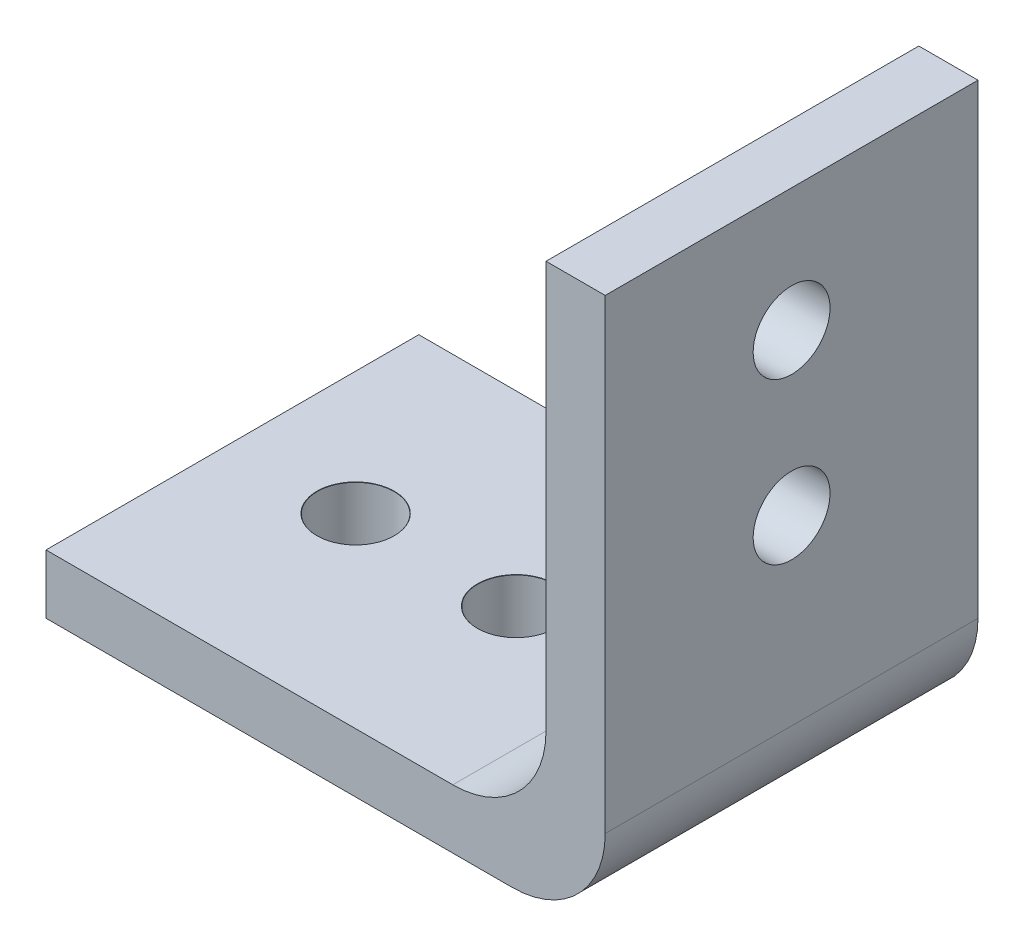
SolidWorks part; units mm, degrees
ref_plane "Front Plane" through (0, 0, 0) normal (0, 0, 1) x (1, 0, 0)
ref_plane "Top Plane" through (0, 0, 0) normal (0, 1, 0) x (1, 0, 0)
ref_plane "Right Plane" through (0, 0, 0) normal (1, 0, 0) x (0, 0, -1)
sketch "Sketch1" plane through (0, 0, 0) normal (0, 1, 0) x (1, 0, 0)
  line L1 (-18.3871, 16.4043) -> (41.6129, 16.4043)
  line L2 (-18.3871, 16.4043) -> (-18.3871, -23.5957)
  line L3 (-18.3871, -23.5957) -> (41.6129, -23.5957)
  line L4 (41.6129, 16.4043) -> (41.6129, -23.5957)
  dimension "D1" = 60
  dimension "D2" = 40
  dimension "D3" = 18.3871
  dimension "D4" = 16.4043
extrude "Boss-Extrude1" add sketch "Sketch1" along normal blind 6.35
sketch "Sketch2" plane through (0, 6.35, 0) normal (0, 1, 0) x (1, 0, 0)
  line L0 (41.6129, 16.4043) -> (-18.3871, 16.4043) construction
  line L1 (35.2629, 16.4043) -> (41.6129, 16.4043)
  line L2 (35.2629, 16.4043) -> (35.2629, -23.5957)
  line L3 (35.2629, -23.5957) -> (41.6129, -23.5957)
  line L4 (41.6129, 16.4043) -> (41.6129, -23.5957)
  line L5 (41.6129, -23.5957) -> (41.6129, 16.4043) construction
  line L6 (-18.3871, -23.5957) -> (41.6129, -23.5957) construction
  dimension "D1" = 0
  dimension "D2" = 0
  dimension "D3" = 0
  dimension "D4" = 6.35
extrude "Boss-Extrude2" add sketch "Sketch2" along normal blind 53.65 contours L2 L1 L4 L3
fillet "Fillet4" radius 10 1 edges at (35.2629, 6.35, 3.5957)
fillet "Fillet5" radius 10 1 edges at (41.6129, 0, 3.5957)
hole_wizard "Tap Drill for M8 Helicoil1" positions "Sketch5" profile "Sketch6" hole size "M8x1.0" standard "ANSI Metric" end condition through all
sketch "Sketch5" plane through (0, 6.35, 0) normal (0, 1, 0) x (1, 0, 0)
  line L0 (-18.3871, 16.4043) -> (-18.3871, -23.5957) construction
  line L2 (25.2629, 16.4043) -> (-18.3871, 16.4043) construction
  point P0 (12.0529, -3.5957)
  point P2 (-5.1671, -3.5957)
  dimension "D1" = 13.22
  dimension "D2" = 17.22
  dimension "D3" = 20
  dimension "D4" = 20
sketch "Sketch6" plane through (12.0529, 6.35, 3.5957) normal (1, 0, 0) x (0, 0, 1)
  line L0 (0, 0) -> (0, 6.35)
  line L1 (0, 6.35) -> (4.125, 6.35)
  line L2 (4.125, 6.35) -> (4.125, 0.025)
  line L3 (4.125, 0.025) -> (4.15, 0)
  line L5 (4.15, 0) -> (0, 0)
  line L6 (-4.125, 0.025) -> (-4.15, 0) construction
  line L11 (0, -6.35) -> (0, 107.95) construction
  dimension "Thru Hole Dia." = 8.25
  dimension "Thru Hole Depth" = 6.35
  dimension "Near C'Sink Dia." = 8.3
  dimension "Near C'Sink Angle" = 90
hole_wizard "Tap Drill for M8 Helicoil2" positions "Sketch7" profile "Sketch8" hole size "M8x1.0" standard "ANSI Metric" end condition through all
sketch "Sketch7" plane through (35.2629, 0, 0) normal (-1, 0, 0) x (0, 0, 1)
  line L0 (-16.4043, 60) -> (23.5957, 60) construction
  line L1 (23.5957, 60) -> (23.5957, 16.35) construction
  point P0 (3.5957, 46.78)
  point P2 (3.5957, 29.56)
  dimension "D1" = 13.22
  dimension "D2" = 20
  dimension "D3" = 20
  dimension "D4" = 17.22
sketch "Sketch8" plane through (35.2629, 46.78, 3.5957) normal (0, 1, 0) x (0, 0, 1)
  line L0 (0, 0) -> (0, 6.35)
  line L1 (0, 6.35) -> (4.125, 6.35)
  line L2 (4.125, 6.35) -> (4.125, 0.025)
  line L3 (4.125, 0.025) -> (4.15, 0)
  line L5 (4.15, 0) -> (0, 0)
  line L6 (-4.125, 0.025) -> (-4.15, 0) construction
  line L11 (0, -6.35) -> (0, 107.95) construction
  dimension "Thru Hole Dia." = 8.25
  dimension "Thru Hole Depth" = 6.35
  dimension "Near C'Sink Dia." = 8.3
  dimension "Near C'Sink Angle" = 90
